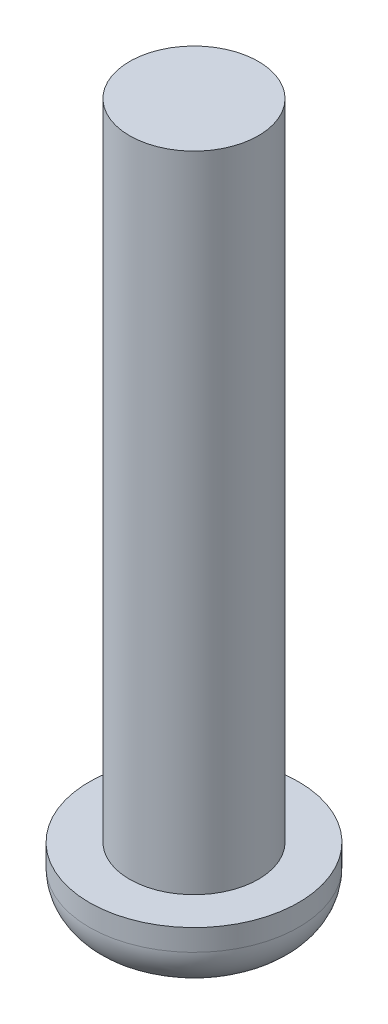
SolidWorks part; units mm, degrees
ref_plane "前视基准面" through (0, 0, 0) normal (0, 0, 1) x (1, 0, 0)
ref_plane "上视基准面" through (0, 0, 0) normal (0, 1, 0) x (1, 0, 0)
ref_plane "右视基准面" through (0, 0, 0) normal (1, 0, 0) x (0, 0, -1)
sketch "草图1" plane through (0, 0, 0) normal (0, 0, 1) x (1, 0, 0)
  line L0 (36.5, 4) -> (30, 4)
  line L1 (30, 4) -> (30, 0)
  line L2 (30, 0) -> (36.5, 0)
  line L3 (36.5, 0) -> (36.5, 4)
  line L4 (30, 4) -> (30, 0) construction
revolve "旋转1" add sketch "草图1" angle 360 about L4
sketch "草图2" plane through (0, 4, 0) normal (0, 1, 0) x (-1, 0, 0)
  circle A0 centre (-30, 0) radius 4
extrude "凸台-拉伸1" add sketch "草图2" along normal blind 40
sketch "草图3" plane through (0, 0, 0) normal (0, -1, 0) x (1, 0, 0)
  line L0 (28.75, -2.1651) -> (31.25, -2.1651)
  line L1 (31.25, -2.1651) -> (32.5, 0)
  line L2 (32.5, 0) -> (31.25, 2.1651)
  line L3 (31.25, 2.1651) -> (28.75, 2.1651)
  line L4 (28.75, 2.1651) -> (27.5, 0)
  line L5 (27.5, 0) -> (28.75, -2.1651)
extrude "切除-拉伸1" cut sketch "草图3" against normal blind 2
fillet "圆角1" radius 2.6667 1 edges at (30, 0, -6.5)
